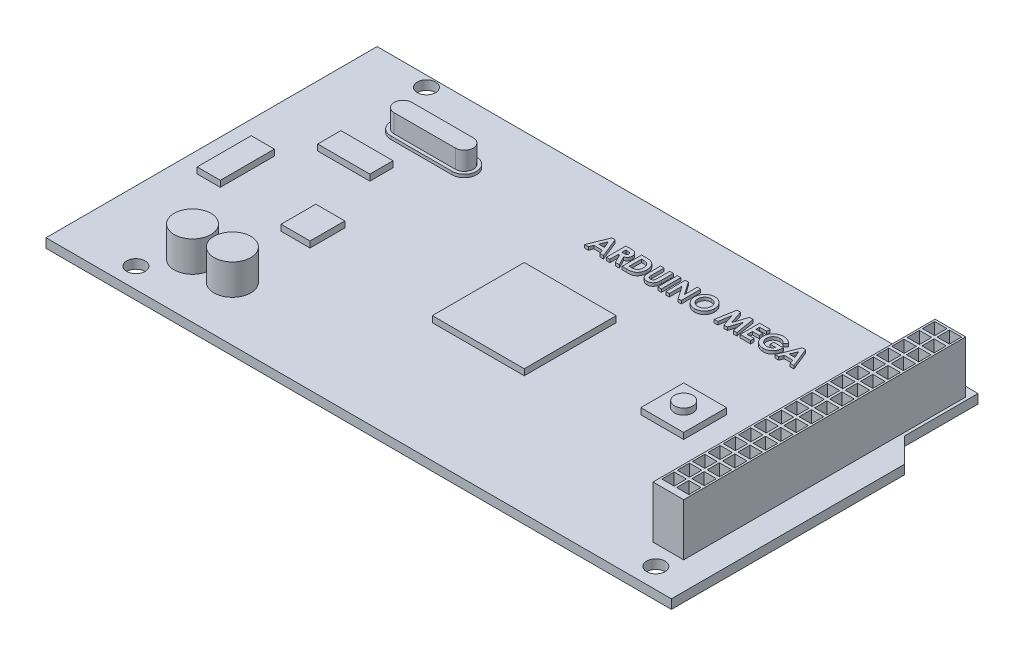
SolidWorks part; units mm, degrees
material "ABS"
ref_plane "Front Plane" through (0, 0, 0) normal (0, 0, 1) x (1, 0, 0)
ref_plane "Top Plane" through (0, 0, 0) normal (0, 1, 0) x (1, 0, 0)
ref_plane "Right Plane" through (0, 0, 0) normal (1, 0, 0) x (0, 0, -1)
sketch "Sketch1" plane through (0, 0, 0) normal (0, 1, 0) x (1, 0, 0)
  line L1 (-51, 27) -> (51, 27)
  line L2 (-51, 27) -> (-51, -27)
  line L3 (-51, -27) -> (51, -27)
  line L4 (51, 27) -> (51, -27)
  line L5 (-51, 27) -> (51, -27) construction
  line L6 (-51, -27) -> (51, 27) construction
  point P0 (0, 0)
  dimension "D1" = 102
  dimension "D2" = 54
extrude "Boss-Extrude1" add sketch "Sketch1" along normal blind 1.5
sketch "Sketch2" plane through (0, 1.5, 0) normal (0, 1, 0) x (1, 0, 0)
  line L0 (51, 27) -> (47, 27) construction
  line L1 (51, 27) -> (-51, 27) construction
  line L2 (47, 27) -> (47, 15)
  line L3 (51, 27) -> (51, 11)
  line L4 (51, -27) -> (51, 27) construction
  line L5 (47, 15) -> (51, 11)
  line L6 (51, 27) -> (47, 27)
  dimension "D1" = 4
  dimension "D2" = 12
  dimension "D3" = 16
extrude "Cut-Extrude1" cut sketch "Sketch2" against normal blind 1.5
sketch "Sketch3" plane through (0, 1.5, 0) normal (0, 1, 0) x (1, 0, 0)
  line L0 (51, -27) -> (51, 11) construction
  line L1 (41.5, 25.5) -> (46.5, 25.5)
  line L2 (41.5, 25.5) -> (41.5, -20.5)
  line L3 (41.5, -20.5) -> (46.5, -20.5)
  line L4 (46.5, 25.5) -> (46.5, -20.5)
  line L5 (41.5, 25.5) -> (46.5, -20.5) construction
  line L6 (41.5, -20.5) -> (46.5, 25.5) construction
  line L7 (47, 27) -> (-51, 27) construction
  point P0 (44, 2.5)
  dimension "D1" = 5
  dimension "D2" = 46
  dimension "D3" = 7
  dimension "D4" = 1.5
extrude "Boss-Extrude2" add sketch "Sketch3" along normal blind 8.5
sketch "Sketch4" plane through (0, 10, 0) normal (0, 1, 0) x (1, 0, 0)
  line L0 (44, 25.5) -> (44, -20.5) construction
  line L1 (46.5, 25.5) -> (41.5, 25.5) construction
  line L2 (41.5, -20.5) -> (46.5, -20.5) construction
  line L3 (44, 25.5) -> (41.5, 25.5) construction
  line L4 (44.1971, 25.138) -> (44.1971, 23.138)
  line L5 (41.8029, 25.138) -> (43.8029, 25.138)
  line L6 (41.8029, 25.138) -> (41.8029, 23.138)
  line L7 (41.8029, 23.138) -> (43.8029, 23.138)
  line L8 (43.8029, 25.138) -> (43.8029, 23.138)
  line L9 (41.8029, 25.138) -> (43.8029, 23.138) construction
  line L10 (41.8029, 23.138) -> (43.8029, 25.138) construction
  line L11 (46.1971, 25.138) -> (44.1971, 25.138)
  line L12 (46.1971, 25.138) -> (46.1971, 23.138)
  line L13 (46.1971, 23.138) -> (44.1971, 23.138)
  line L14 (41.8029, 20.638) -> (43.8029, 20.638)
  line L15 (41.8029, 22.638) -> (41.8029, 20.638)
  line L16 (41.8029, 22.638) -> (43.8029, 22.638)
  line L17 (43.8029, 22.638) -> (43.8029, 20.638)
  line L18 (46.1971, 22.638) -> (44.1971, 22.638)
  line L19 (44.1971, 22.638) -> (44.1971, 20.638)
  line L20 (46.1971, 20.638) -> (44.1971, 20.638)
  line L21 (46.1971, 22.638) -> (46.1971, 20.638)
  line L22 (41.8029, 18.138) -> (43.8029, 18.138)
  line L23 (41.8029, 20.138) -> (41.8029, 18.138)
  line L24 (41.8029, 20.138) -> (43.8029, 20.138)
  line L25 (43.8029, 20.138) -> (43.8029, 18.138)
  line L26 (46.1971, 20.138) -> (44.1971, 20.138)
  line L27 (44.1971, 20.138) -> (44.1971, 18.138)
  line L28 (46.1971, 18.138) -> (44.1971, 18.138)
  line L29 (46.1971, 20.138) -> (46.1971, 18.138)
  line L30 (41.8029, 15.638) -> (43.8029, 15.638)
  line L31 (41.8029, 17.638) -> (41.8029, 15.638)
  line L32 (41.8029, 17.638) -> (43.8029, 17.638)
  line L33 (43.8029, 17.638) -> (43.8029, 15.638)
  line L34 (46.1971, 17.638) -> (44.1971, 17.638)
  line L35 (44.1971, 17.638) -> (44.1971, 15.638)
  line L36 (46.1971, 15.638) -> (44.1971, 15.638)
  line L37 (46.1971, 17.638) -> (46.1971, 15.638)
  line L38 (41.8029, 13.138) -> (43.8029, 13.138)
  line L39 (41.8029, 15.138) -> (41.8029, 13.138)
  line L40 (41.8029, 15.138) -> (43.8029, 15.138)
  line L41 (43.8029, 15.138) -> (43.8029, 13.138)
  line L42 (46.1971, 15.138) -> (44.1971, 15.138)
  line L43 (44.1971, 15.138) -> (44.1971, 13.138)
  line L44 (46.1971, 13.138) -> (44.1971, 13.138)
  line L45 (46.1971, 15.138) -> (46.1971, 13.138)
  line L46 (41.8029, 10.638) -> (43.8029, 10.638)
  line L47 (41.8029, 12.638) -> (41.8029, 10.638)
  line L48 (41.8029, 12.638) -> (43.8029, 12.638)
  line L49 (43.8029, 12.638) -> (43.8029, 10.638)
  line L50 (46.1971, 12.638) -> (44.1971, 12.638)
  line L51 (44.1971, 12.638) -> (44.1971, 10.638)
  line L52 (46.1971, 10.638) -> (44.1971, 10.638)
  line L53 (46.1971, 12.638) -> (46.1971, 10.638)
  line L54 (41.8029, 8.138) -> (43.8029, 8.138)
  line L55 (41.8029, 10.138) -> (41.8029, 8.138)
  line L56 (41.8029, 10.138) -> (43.8029, 10.138)
  line L57 (43.8029, 10.138) -> (43.8029, 8.138)
  line L58 (46.1971, 10.138) -> (44.1971, 10.138)
  line L59 (44.1971, 10.138) -> (44.1971, 8.138)
  line L60 (46.1971, 8.138) -> (44.1971, 8.138)
  line L61 (46.1971, 10.138) -> (46.1971, 8.138)
  line L62 (41.8029, 5.638) -> (43.8029, 5.638)
  line L63 (41.8029, 7.638) -> (41.8029, 5.638)
  line L64 (41.8029, 7.638) -> (43.8029, 7.638)
  line L65 (43.8029, 7.638) -> (43.8029, 5.638)
  line L66 (46.1971, 7.638) -> (44.1971, 7.638)
  line L67 (44.1971, 7.638) -> (44.1971, 5.638)
  line L68 (46.1971, 5.638) -> (44.1971, 5.638)
  line L69 (46.1971, 7.638) -> (46.1971, 5.638)
  line L70 (41.8029, 3.138) -> (43.8029, 3.138)
  line L71 (41.8029, 5.138) -> (41.8029, 3.138)
  line L72 (41.8029, 5.138) -> (43.8029, 5.138)
  line L73 (43.8029, 5.138) -> (43.8029, 3.138)
  line L74 (46.1971, 5.138) -> (44.1971, 5.138)
  line L75 (44.1971, 5.138) -> (44.1971, 3.138)
  line L76 (46.1971, 3.138) -> (44.1971, 3.138)
  line L77 (46.1971, 5.138) -> (46.1971, 3.138)
  line L78 (41.8029, 0.638) -> (43.8029, 0.638)
  line L79 (41.8029, 2.638) -> (41.8029, 0.638)
  line L80 (41.8029, 2.638) -> (43.8029, 2.638)
  line L81 (43.8029, 2.638) -> (43.8029, 0.638)
  line L82 (46.1971, 2.638) -> (44.1971, 2.638)
  line L83 (44.1971, 2.638) -> (44.1971, 0.638)
  line L84 (46.1971, 0.638) -> (44.1971, 0.638)
  line L85 (46.1971, 2.638) -> (46.1971, 0.638)
  line L86 (41.8029, -1.862) -> (43.8029, -1.862)
  line L87 (41.8029, 0.138) -> (41.8029, -1.862)
  line L88 (41.8029, 0.138) -> (43.8029, 0.138)
  line L89 (43.8029, 0.138) -> (43.8029, -1.862)
  line L90 (46.1971, 0.138) -> (44.1971, 0.138)
  line L91 (44.1971, 0.138) -> (44.1971, -1.862)
  line L92 (46.1971, -1.862) -> (44.1971, -1.862)
  line L93 (46.1971, 0.138) -> (46.1971, -1.862)
  line L94 (41.8029, -4.362) -> (43.8029, -4.362)
  line L95 (41.8029, -2.362) -> (41.8029, -4.362)
  line L96 (41.8029, -2.362) -> (43.8029, -2.362)
  line L97 (43.8029, -2.362) -> (43.8029, -4.362)
  line L98 (46.1971, -2.362) -> (44.1971, -2.362)
  line L99 (44.1971, -2.362) -> (44.1971, -4.362)
  line L100 (46.1971, -4.362) -> (44.1971, -4.362)
  line L101 (46.1971, -2.362) -> (46.1971, -4.362)
  line L102 (41.8029, -6.862) -> (43.8029, -6.862)
  line L103 (41.8029, -4.862) -> (41.8029, -6.862)
  line L104 (41.8029, -4.862) -> (43.8029, -4.862)
  line L105 (43.8029, -4.862) -> (43.8029, -6.862)
  line L106 (46.1971, -4.862) -> (44.1971, -4.862)
  line L107 (44.1971, -4.862) -> (44.1971, -6.862)
  line L108 (46.1971, -6.862) -> (44.1971, -6.862)
  line L109 (46.1971, -4.862) -> (46.1971, -6.862)
  line L110 (41.8029, -9.362) -> (43.8029, -9.362)
  line L111 (41.8029, -7.362) -> (41.8029, -9.362)
  line L112 (41.8029, -7.362) -> (43.8029, -7.362)
  line L113 (43.8029, -7.362) -> (43.8029, -9.362)
  line L114 (46.1971, -7.362) -> (44.1971, -7.362)
  line L115 (44.1971, -7.362) -> (44.1971, -9.362)
  line L116 (46.1971, -9.362) -> (44.1971, -9.362)
  line L117 (46.1971, -7.362) -> (46.1971, -9.362)
  line L118 (41.8029, -11.862) -> (43.8029, -11.862)
  line L119 (41.8029, -9.862) -> (41.8029, -11.862)
  line L120 (41.8029, -9.862) -> (43.8029, -9.862)
  line L121 (43.8029, -9.862) -> (43.8029, -11.862)
  line L122 (46.1971, -9.862) -> (44.1971, -9.862)
  line L123 (44.1971, -9.862) -> (44.1971, -11.862)
  line L124 (46.1971, -11.862) -> (44.1971, -11.862)
  line L125 (46.1971, -9.862) -> (46.1971, -11.862)
  line L126 (41.8029, -14.362) -> (43.8029, -14.362)
  line L127 (41.8029, -12.362) -> (41.8029, -14.362)
  line L128 (41.8029, -12.362) -> (43.8029, -12.362)
  line L129 (43.8029, -12.362) -> (43.8029, -14.362)
  line L130 (46.1971, -12.362) -> (44.1971, -12.362)
  line L131 (44.1971, -12.362) -> (44.1971, -14.362)
  line L132 (46.1971, -14.362) -> (44.1971, -14.362)
  line L133 (46.1971, -12.362) -> (46.1971, -14.362)
  line L134 (41.8029, -16.862) -> (43.8029, -16.862)
  line L135 (41.8029, -14.862) -> (41.8029, -16.862)
  line L136 (41.8029, -14.862) -> (43.8029, -14.862)
  line L137 (43.8029, -14.862) -> (43.8029, -16.862)
  line L138 (46.1971, -14.862) -> (44.1971, -14.862)
  line L139 (44.1971, -14.862) -> (44.1971, -16.862)
  line L140 (46.1971, -16.862) -> (44.1971, -16.862)
  line L141 (46.1971, -14.862) -> (46.1971, -16.862)
  line L142 (41.8029, -19.362) -> (43.8029, -19.362)
  line L143 (41.8029, -17.362) -> (41.8029, -19.362)
  line L144 (41.8029, -17.362) -> (43.8029, -17.362)
  line L145 (43.8029, -17.362) -> (43.8029, -19.362)
  line L146 (46.1971, -17.362) -> (44.1971, -17.362)
  line L147 (44.1971, -17.362) -> (44.1971, -19.362)
  line L148 (46.1971, -19.362) -> (44.1971, -19.362)
  line L149 (46.1971, -17.362) -> (46.1971, -19.362)
  point P6 (42.8029, 24.138)
  dimension "D1" = 2
  dimension "D2" = 2
  dimension "D3" = 18
extrude "Cut-Extrude2" cut sketch "Sketch4" against normal blind 5
sketch "Sketch5" plane through (0, 1.5, 0) normal (0, 1, 0) x (1, 0, 0)
  line L1 (-7.5, 7.5) -> (7.5, 7.5)
  line L2 (-7.5, 7.5) -> (-7.5, -7.5)
  line L3 (-7.5, -7.5) -> (7.5, -7.5)
  line L4 (7.5, 7.5) -> (7.5, -7.5)
  line L5 (-7.5, 7.5) -> (7.5, -7.5) construction
  line L6 (-7.5, -7.5) -> (7.5, 7.5) construction
  point P0 (0, 0)
  dimension "D1" = 15
  dimension "D2" = 15
extrude "Boss-Extrude3" add sketch "Sketch5" along normal blind 1
sketch "Sketch6" plane through (0, 1.5, 0) normal (0, 1, 0) x (1, 0, 0)
  line L0 (-51, 27) -> (-51, -27) construction
  circle A0 centre (-36, -18.0995) radius 3
  circle A1 centre (-29.5, -18.0995) radius 3
  dimension "D1" = 6
  dimension "D2" = 6.5
  dimension "D3" = 15
extrude "Boss-Extrude4" add sketch "Sketch6" along normal blind 5
sketch "Sketch7" plane through (0, 1.5, 0) normal (0, 1, 0) x (1, 0, 0)
  line L0 (-36.7733, 17) -> (-26.7733, 17) construction
  line L1 (-36.7733, 19) -> (-26.7733, 19)
  line L2 (-36.7733, 15) -> (-26.7733, 15)
  line L3 (47, 27) -> (-51, 27) construction
  arc A0 (-36.7733, 19) -> (-36.7733, 15) centre (-36.7733, 17) ccw
  arc A1 (-26.7733, 15) -> (-26.7733, 19) centre (-26.7733, 17) ccw
  point P2 (-31.7733, 17)
  dimension "D1" = 4
  dimension "D2" = 10
  dimension "D3" = 8
extrude "Boss-Extrude5" add sketch "Sketch7" along normal blind 0.5
sketch "Sketch8" plane through (0, 1.5, 0) normal (0, 1, 0) x (1, 0, 0)
  line L1 (-41.0781, 11.1745) -> (-32.5792, 11.1745)
  line L2 (-41.0781, 11.1745) -> (-41.0781, 7.3972)
  line L3 (-41.0781, 7.3972) -> (-32.5792, 7.3972)
  line L4 (-32.5792, 11.1745) -> (-32.5792, 7.3972)
  line L5 (-41.0781, 11.1745) -> (-32.5792, 7.3972) construction
  line L6 (-41.0781, 7.3972) -> (-32.5792, 11.1745) construction
  point P0 (-36.8286, 9.2858)
extrude "Boss-Extrude6" add sketch "Sketch8" along normal blind 1
sketch "Sketch9" plane through (0, 1.5, 0) normal (0, 1, 0) x (1, 0, 0)
  line L1 (-32.7365, -1.2591) -> (-28.0149, -1.2591)
  line L2 (-32.7365, -1.2591) -> (-32.7365, -6.925)
  line L3 (-32.7365, -6.925) -> (-28.0149, -6.925)
  line L4 (-28.0149, -1.2591) -> (-28.0149, -6.925)
  line L5 (-32.7365, -1.2591) -> (-28.0149, -6.925) construction
  line L6 (-32.7365, -6.925) -> (-28.0149, -1.2591) construction
  point P0 (-30.3757, -4.0921)
extrude "Boss-Extrude7" add sketch "Sketch9" along normal blind 1
sketch "Sketch10" plane through (0, 1.5, 0) normal (0, 1, 0) x (1, 0, 0)
  circle A0 centre (45.1436, -23.6847) radius 1.5
  dimension "D1" = 3
extrude "Cut-Extrude3" cut sketch "Sketch10" against normal blind 11
sketch "Sketch11" plane through (0, 1.5, 0) normal (0, 1, 0) x (1, 0, 0)
  circle A0 centre (39.5472, 25.2672) radius 1.5
  dimension "D1" = 3
extrude "Cut-Extrude4" cut sketch "Sketch11" against normal blind 11
sketch "Sketch12" plane through (0, 1.5, 0) normal (0, 1, 0) x (1, 0, 0)
  circle A0 centre (-41.2178, 25.2672) radius 1.5
  dimension "D1" = 3
extrude "Cut-Extrude5" cut sketch "Sketch12" against normal blind 11
sketch "Sketch13" plane through (0, 1.5, 0) normal (0, 1, 0) x (1, 0, 0)
  circle A0 centre (-39.6616, -23.6847) radius 1.5
  dimension "D1" = 3
extrude "Cut-Extrude6" cut sketch "Sketch13" against normal blind 11
sketch "Sketch14" plane through (0, 1.5, 0) normal (0, 1, 0) x (1, 0, 0)
  line L0 (0, 0) -> (36.9922, 0) construction
  line L1 (7.5, -7.5) -> (7.5, 7.5) construction
  line L2 (22.5, 3.5) -> (29.5, 3.5)
  line L3 (22.5, 3.5) -> (22.5, -3.5)
  line L4 (22.5, -3.5) -> (29.5, -3.5)
  line L5 (29.5, 3.5) -> (29.5, -3.5)
  line L6 (22.5, 3.5) -> (29.5, -3.5) construction
  line L7 (22.5, -3.5) -> (29.5, 3.5) construction
  point P3 (26, 0)
  dimension "D1" = 7
  dimension "D2" = 7
  dimension "D3" = 15
extrude "Boss-Extrude8" add sketch "Sketch14" along normal blind 1
sketch "Sketch15" plane through (0, 2.5, 0) normal (0, 1, 0) x (1, 0, 0)
  line L1 (7.5, -7.5) -> (7.5, 7.5) construction
  circle A0 centre (26, 0) radius 1.5
  dimension "D1" = 3
  dimension "D2" = 18.5
extrude "Boss-Extrude9" add sketch "Sketch15" along normal blind 1
sketch "Sketch16" plane through (0, 1.5, 0) normal (0, 1, 0) x (1, 0, 0)
  line L1 (-47.6785, 3.146) -> (-43.8988, 3.146)
  line L2 (-47.6785, 3.146) -> (-47.6785, -5.6732)
  line L3 (-47.6785, -5.6732) -> (-43.8988, -5.6732)
  line L4 (-43.8988, 3.146) -> (-43.8988, -5.6732)
  line L5 (-47.6785, 3.146) -> (-43.8988, -5.6732) construction
  line L6 (-47.6785, -5.6732) -> (-43.8988, 3.146) construction
  point P0 (-45.7886, -1.2636)
extrude "Boss-Extrude10" add sketch "Sketch16" along normal blind 1
sketch "Sketch17" plane through (0, 1.5, 0) normal (0, 1, 0) x (1, 0, 0)
  text T0 "<b>ARDUINO MEGA</b>"
extrude "Boss-Extrude11" add sketch "Sketch17" along normal blind 0.5
sketch "Sketch18" plane through (0, 2, 0) normal (0, 1, 0) x (1, 0, 0)
  line L0 (-36.7733, 17) -> (-26.7733, 17) construction
  line L1 (-36.7733, 18.4519) -> (-26.7733, 18.4519)
  line L2 (-36.7733, 15.5481) -> (-26.7733, 15.5481)
  arc A0 (-36.7733, 18.4519) -> (-36.7733, 15.5481) centre (-36.7733, 17) ccw
  arc A1 (-26.7733, 15.5481) -> (-26.7733, 18.4519) centre (-26.7733, 17) ccw
  point P4 (-31.7733, 17)
extrude "Boss-Extrude12" add sketch "Sketch18" along normal blind 3
